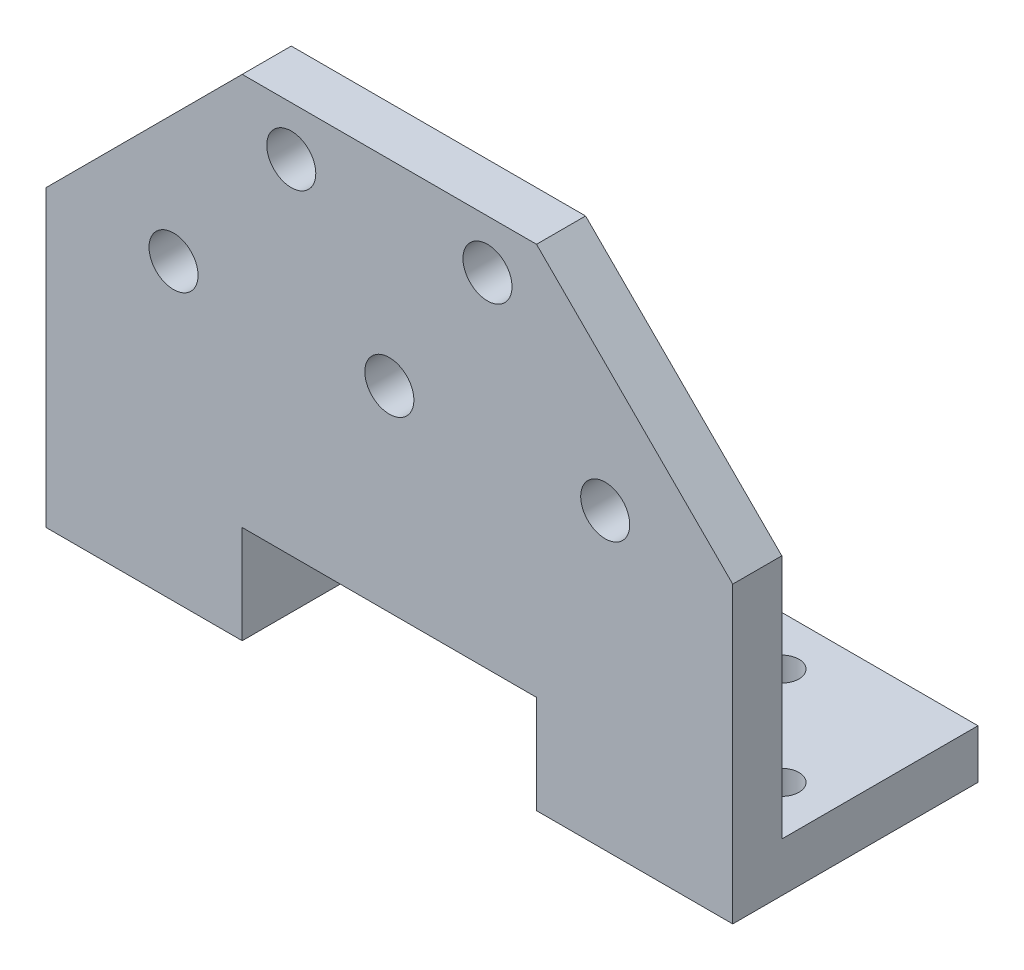
SolidWorks part; units mm, degrees
ref_plane "正面(Front)" through (0, 0, 0) normal (0, 0, 1) x (1, 0, 0)
ref_plane "平面(Top)" through (0, 0, 0) normal (0, 1, 0) x (1, 0, 0)
ref_plane "右側面(Right)" through (0, 0, 0) normal (1, 0, 0) x (0, 0, -1)
sketch "ｽｹｯﾁ1" plane through (0, 0, 0) normal (0, 0, 1) x (1, 0, 0)
  line L0 (0, 0) -> (0, 52.0615) construction
  line L1 (0, 0) -> (63.1908, 0) construction
  line L2 (-15, 10) -> (15, 10)
  line L3 (15, 10) -> (15, 0)
  line L4 (15, 0) -> (35, 0)
  line L5 (35, 0) -> (35, 50)
  line L6 (35, 50) -> (-35, 50)
  line L7 (-35, 0) -> (-35, 50)
  line L8 (-15, 0) -> (-35, 0)
  line L9 (-15, 10) -> (-15, 0)
  point P11 (0, 50)
  point P14 (0, 10)
  dimension "D1" = 70
  dimension "D2" = 30
  dimension "D3" = 10
  dimension "D4" = 50
extrude "ﾎﾞｽ - 押し出し1" add sketch "ｽｹｯﾁ1" along normal blind 5
sketch "ｽｹｯﾁ3" plane through (0, 0, 0) normal (0, 1, 0) x (1, 0, 0)
  line L1 (-35, 0) -> (-15, 0)
  line L2 (-35, 0) -> (-35, 20)
  line L3 (-35, 20) -> (-15, 20)
  line L4 (-15, 0) -> (-15, 20)
  line L5 (35, 0) -> (15, 0)
  line L6 (35, 0) -> (35, 20)
  line L7 (35, 20) -> (15, 20)
  line L8 (15, 0) -> (15, 20)
  dimension "D1" = 20
extrude "ﾎﾞｽ - 押し出し2" add sketch "ｽｹｯﾁ3" along normal blind 5
sketch "ｽｹｯﾁ4" plane through (0, 5, 0) normal (0, 1, 0) x (1, 0, 0)
  line L0 (-35, 20) -> (-35, 0) construction
  line L1 (-35, 0) -> (-15, 0) construction
  line L2 (-15, 0) -> (-15, 20) construction
  line L3 (-15, 20) -> (-35, 20) construction
  line L4 (0, 0) -> (0, 19.0502) construction
  line L5 (35, 0) -> (-35, 0) construction
  circle A0 centre (-30, 5) radius 1.75
  circle A1 centre (-20, 15) radius 1.75
  circle A2 centre (20, 15) radius 1.75
  circle A3 centre (30, 5) radius 1.75
  dimension "D1" = 3.5
  dimension "D2" = 5
  dimension "D3" = 5
  dimension "D4" = 5
  dimension "D5" = 5
extrude "ｶｯﾄ - 押し出し1" cut sketch "ｽｹｯﾁ4" against normal through all
sketch "ｽｹｯﾁ5" plane through (0, 0, 5) normal (0, 0, 1) x (1, 0, 0)
  line L0 (0, 0) -> (0, 57.2223) construction
  line L1 (35, 30) -> (15, 50)
  line L2 (35, 0) -> (35, 50) construction
  line L3 (35, 50) -> (-35, 50) construction
  line L4 (-35, 30) -> (-15, 50)
  line L5 (-15, 50) -> (15, 50)
  dimension "D1" = 20
  dimension "D2" = 45
extrude "ｶｯﾄ - 押し出し2" cut sketch "ｽｹｯﾁ5" against normal through all and the other way through all
sketch "ｽｹｯﾁ6" plane through (0, 0, 0) normal (0, 0, -1) x (-1, 0, 0)
  line L0 (-35, 30) -> (29.4204, 30) construction
  line L1 (-35, 5) -> (-35, 30) construction
  line L2 (-15, 5) -> (-35, 5) construction
  line L3 (0, 0) -> (0, 56.8407) construction
  circle A0 centre (-22, 30) radius 2.5
  circle A1 centre (0, 30) radius 2.5
  circle A2 centre (-10, 45) radius 2.5
  circle A3 centre (10, 45) radius 2.5
  circle A4 centre (22, 30) radius 2.5
  dimension "D2" = 5
  dimension "D3" = 22
  dimension "D4" = 10
  dimension "D1" = 25
  dimension "D5" = 15
extrude "ｶｯﾄ - 押し出し3" cut sketch "ｽｹｯﾁ6" against normal through all
